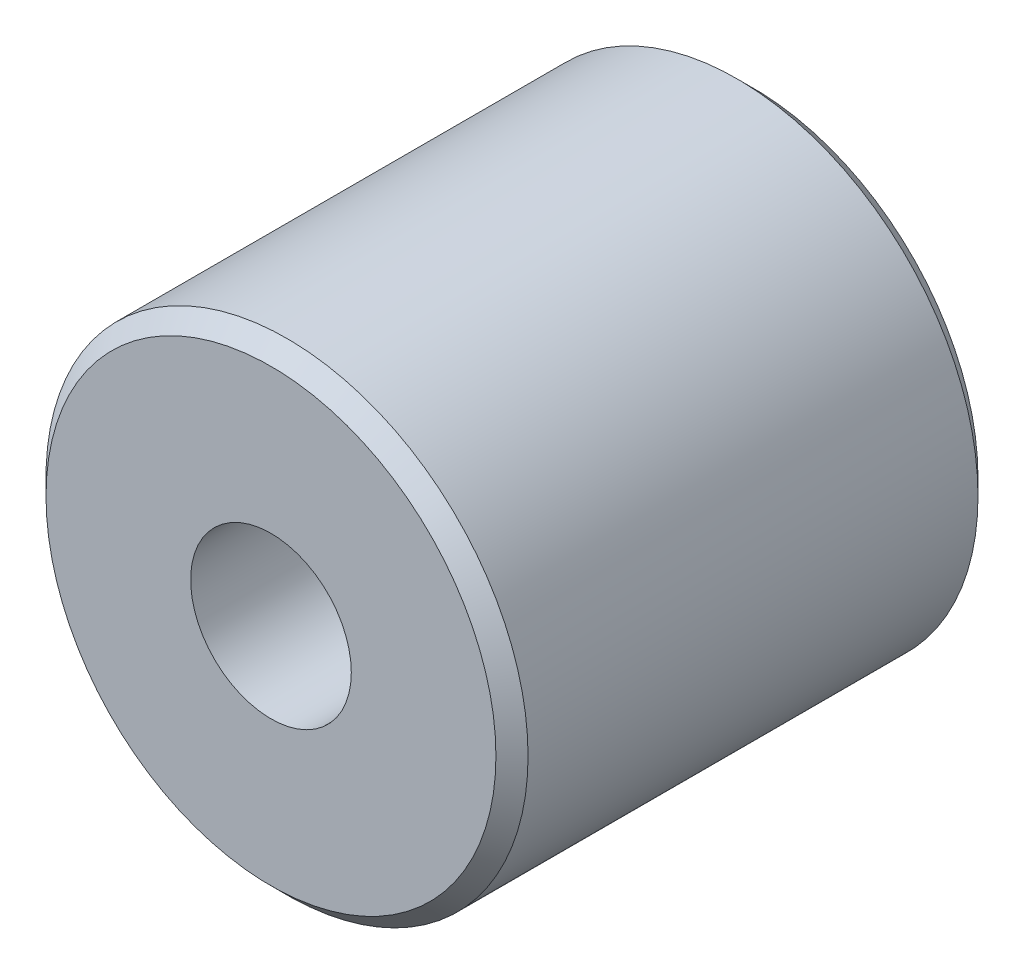
SolidWorks part; units mm, degrees
material "AISI 1020 Steel, Cold Rolled"
ref_plane "Front Plane" through (0, 0, 0) normal (0, 0, 1) x (1, 0, 0)
ref_plane "Top Plane" through (0, 0, 0) normal (0, 1, 0) x (1, 0, 0)
ref_plane "Right Plane" through (0, 0, 0) normal (1, 0, 0) x (0, 0, -1)
sketch "Sketch1" plane through (0, 0, 0) normal (0, 0, 1) x (1, 0, 0)
  circle A0 centre (0, 0) radius 15
  circle A1 centre (0, 0) radius 5
  dimension "D1" = 30
  dimension "D2" = 10
extrude "Boss-Extrude1" add sketch "Sketch1" along normal blind 30
chamfer "Chamfer1" distance 1 angle 45 2 edges at (15, 0, 0) (15, 0, 30)
